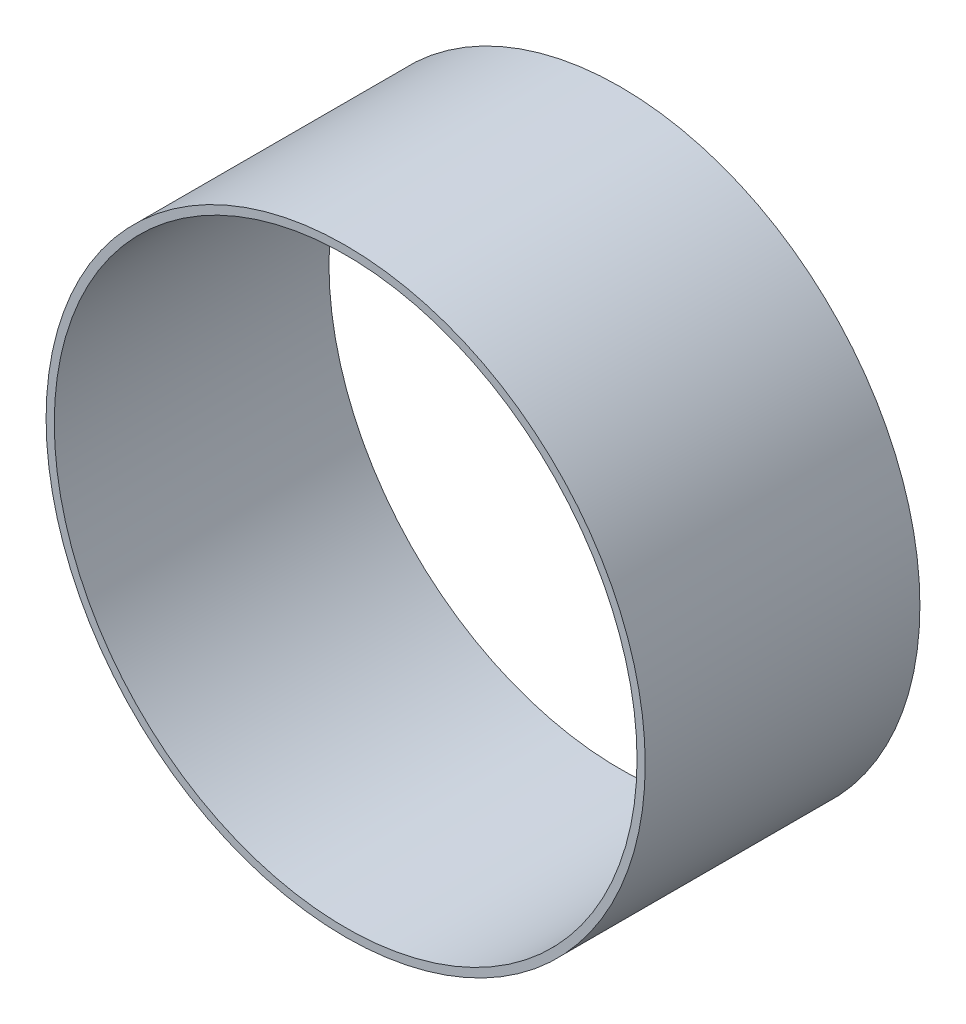
SolidWorks part; units mm, degrees
ref_plane "Front Plane" through (0, 0, 0) normal (0, 0, 1) x (1, 0, 0)
ref_plane "Top Plane" through (0, 0, 0) normal (0, 1, 0) x (1, 0, 0)
ref_plane "Right Plane" through (0, 0, 0) normal (1, 0, 0) x (0, 0, -1)
sketch "Sketch2" plane through (0, 0, 0) normal (0, 0, 1) x (1, 0, 0)
  circle A0 centre (0, 0) radius 22.16
  circle A1 centre (0, 0) radius 21.555
  dimension "D1" = 44.32
extrude "Boss-Extrude1" add sketch "Sketch2" along normal blind 20.32 contours A0
sketch "Sketch3" plane through (0, 0, 20.32) normal (0, 0, 1) x (1, 0, 0)
  circle A0 centre (0, 0) radius 21.555
  dimension "D1" = 43.11
extrude "Cut-Extrude1" cut sketch "Sketch3" against normal blind 20.32
equation "\"ODia\"= 44.32mm"
equation "\"IDia\"= 43.11mm"
equation "\"Length\"= 20.32mm"
equation "\"D1@Sketch2\"=\"ODia\""
equation "\"D1@Boss-Extrude1\"=\"Length\""
equation "\"D1@Sketch3\"=\"IDia\""
